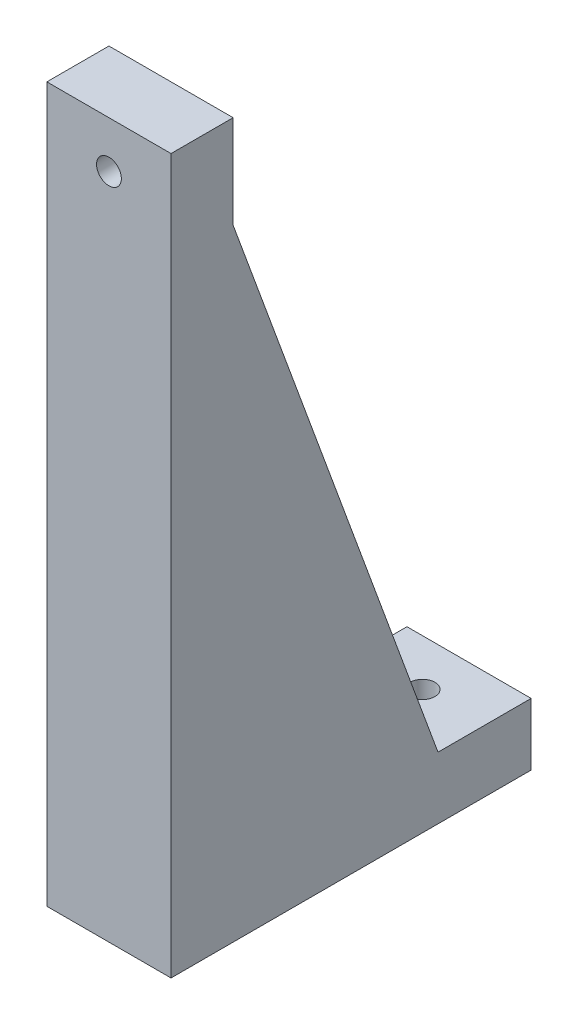
SolidWorks part; units mm, degrees
material "ABS"
ref_plane "Front Plane" through (0, 0, 0) normal (0, 0, 1) x (1, 0, 0)
ref_plane "Top Plane" through (0, 0, 0) normal (0, 1, 0) x (1, 0, 0)
ref_plane "Right Plane" through (0, 0, 0) normal (1, 0, 0) x (0, 0, -1)
sketch "Sketch1" plane through (0, 0, 0) normal (1, 0, 0) x (0, 0, -1)
  line L0 (0, 0) -> (0, 146.05)
  line L1 (0, 146.05) -> (12.7, 146.05)
  line L2 (12.7, 146.05) -> (12.7, 127)
  line L3 (12.7, 127) -> (54.61, 12.7)
  line L4 (54.61, 12.7) -> (73.66, 12.7)
  line L5 (73.66, 12.7) -> (73.66, 0)
  line L6 (73.66, 0) -> (0, 0)
  dimension "D1" = 12.7
  dimension "D2" = 146.05
  dimension "D3" = 73.66
  dimension "D4" = 19.05
extrude "Boss-Extrude1" add sketch "Sketch1" along normal blind 25.4
sketch "Sketch2" plane through (0, 0, -12.7) normal (0, 0, -1) x (-1, 0, 0)
  line L0 (-25.4, 146.05) -> (0, 127) construction
  circle A0 centre (-12.7, 136.525) radius 2.54
  point P4 (-12.7, 136.525)
  dimension "D1" = 5.08
extrude "Cut-Extrude1" cut sketch "Sketch2" against normal through all
sketch "Sketch3" plane through (0, 12.7, 0) normal (0, 1, 0) x (1, 0, 0)
  line L0 (0, 73.66) -> (25.4, 54.61) construction
  circle A0 centre (12.7, 64.135) radius 2.54
  dimension "D1" = 5.08
extrude "Cut-Extrude2" cut sketch "Sketch3" against normal through all
